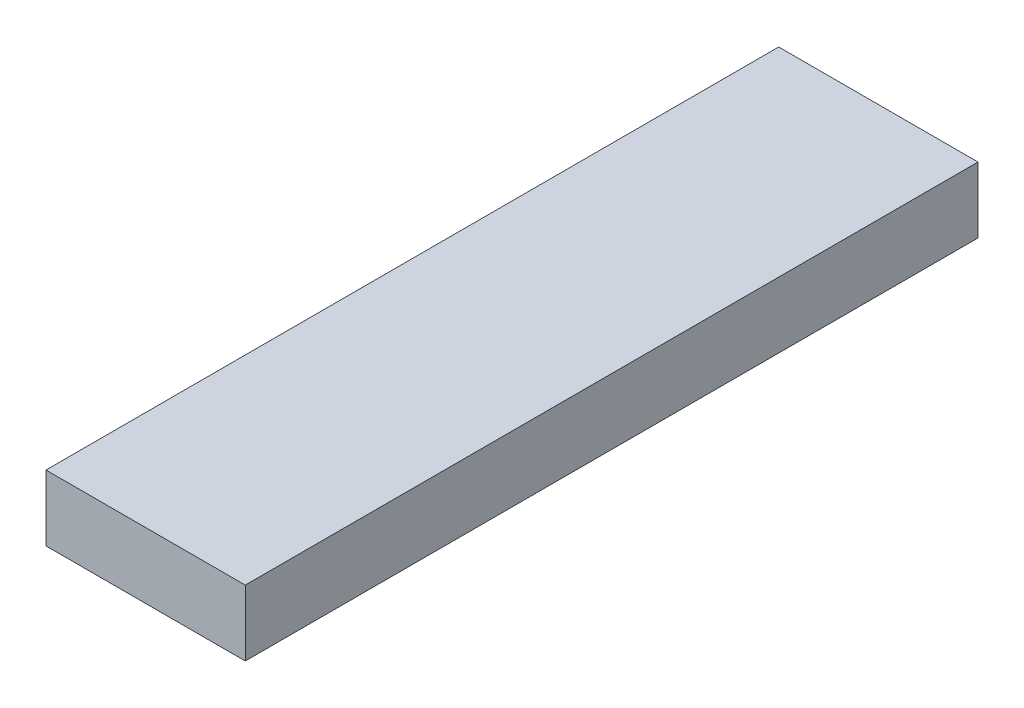
SolidWorks part; units mm, degrees
ref_plane "Front Plane" through (0, 0, 0) normal (0, 0, 1) x (1, 0, 0)
ref_plane "Top Plane" through (0, 0, 0) normal (0, 1, 0) x (1, 0, 0)
ref_plane "Right Plane" through (0, 0, 0) normal (1, 0, 0) x (0, 0, -1)
sketch "Sketch1" plane through (0, 0, 0) normal (0, 1, 0) x (1, 0, 0)
  line L1 (-22.5209, 44.2148) -> (2.8791, 44.2148)
  line L2 (-22.5209, 44.2148) -> (-22.5209, -49.1771)
  line L3 (-22.5209, -49.1771) -> (2.8791, -49.1771)
  line L4 (2.8791, 44.2148) -> (2.8791, -49.1771)
  dimension "D1" = 22.5209
  dimension "D2" = 49.1771
  dimension "D3" = 93.3919
  dimension "D4" = 25.4
extrude "Boss-Extrude1" add sketch "Sketch1" along normal blind 8.382
